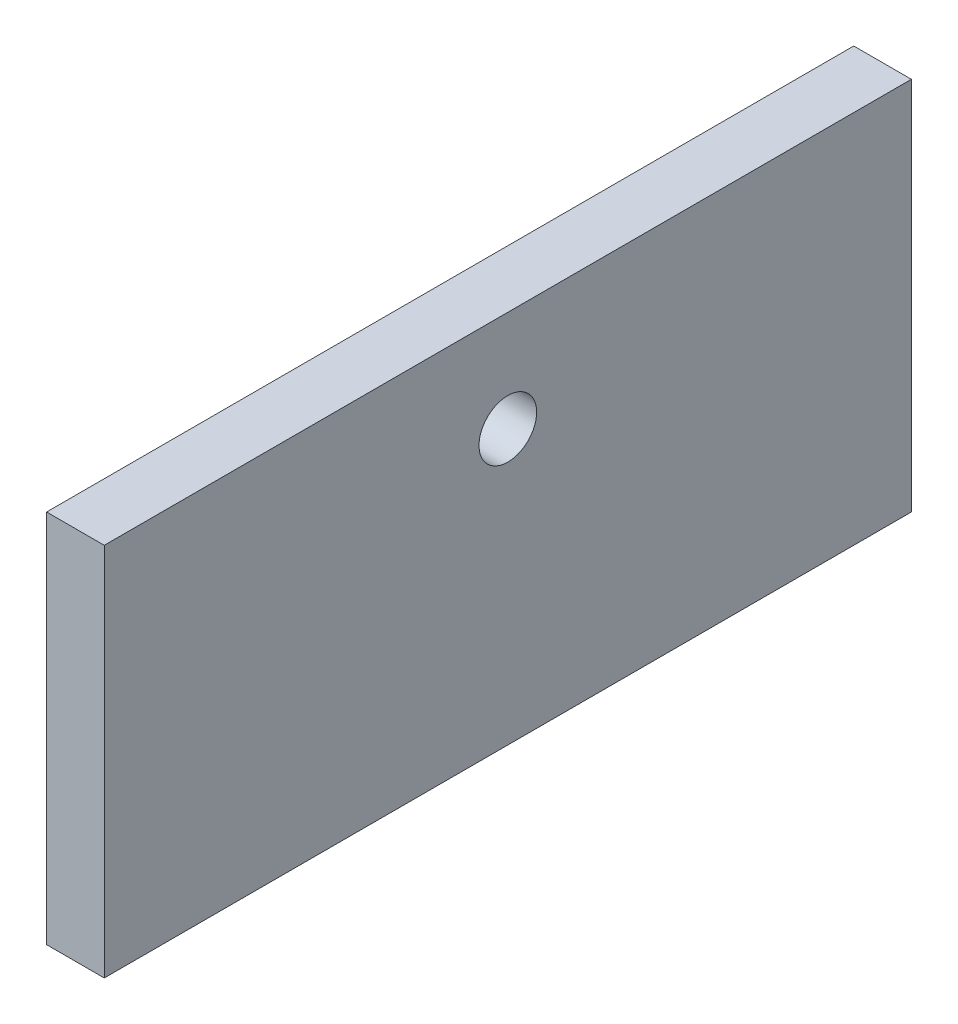
SolidWorks part; units mm, degrees
ref_plane "Front Plane" through (0, 0, 0) normal (0, 0, 1) x (1, 0, 0)
ref_plane "Top Plane" through (0, 0, 0) normal (0, 1, 0) x (1, 0, 0)
ref_plane "Right Plane" through (0, 0, 0) normal (1, 0, 0) x (0, 0, -1)
sketch "Croquis1" plane through (0, 0, 0) normal (1, 0, 0) x (0, 0, -1)
  line L0 (0, 0) -> (0, 25) construction
  circle A0 centre (0, 0) radius 30
  circle A1 centre (0, 0) radius 5
  circle A2 centre (0, 25) radius 2.5
  dimension "D1" = 60
  dimension "D2" = 5
  dimension "D3" = 10
  dimension "D4" = 25
extrude "Saliente-Extruir1" [suppressed] add sketch "Croquis1" along normal blind 10
sketch "Croquis3" plane through (0, 0, 0) normal (0, 0, 1) x (1, 0, 0)
  line L0 (270, 0) -> (-270, 0)
  line L1 (270, 0) -> (270, 5)
  line L2 (270, 5) -> (250, 5)
  line L3 (250, 5) -> (250, 9.5)
  line L4 (250, 9.5) -> (-250, 9.5)
  line L5 (-250, 9.5) -> (-250, 5)
  line L6 (-250, 5) -> (-270, 5)
  line L7 (-270, 5) -> (-270, 0)
  line L8 (-250, 5) -> (250, 5) construction
  point P4 (0, 0)
  dimension "D1" = 500
  dimension "D2" = 20
  dimension "D3" = 20
  dimension "D4" = 5
  dimension "D5" = 9.5
revolve "Revolución1" [suppressed] add sketch "Croquis3" angle 360 about L0
sketch "Croquis4" plane through (0, 0, 0) normal (1, 0, 0) x (0, 0, -1)
  line L1 (50, -30) -> (-50, -30)
  line L2 (50, -30) -> (50, 30)
  line L3 (50, 30) -> (-50, 30)
  line L4 (-50, -30) -> (-50, 30)
  line L5 (50, -30) -> (-50, 30) construction
  line L6 (50, 30) -> (-50, -30) construction
  circle A0 centre (0, 0) radius 9.5
  point P0 (0, 0)
  dimension "D3" = 19
  dimension "D1" = 100
  dimension "D2" = 60
extrude "Saliente-Extruir2" [suppressed] add sketch "Croquis4" along normal blind 50 contours L4 L1 L2 L3 A0
sketch "Croquis5" plane through (0, 0, 0) normal (1, 0, 0) x (0, 0, -1)
  line L0 (50, 0) -> (-50, 0)
  line L1 (-50, 0) -> (-50, 45)
  line L2 (-50, 45) -> (-70, 45)
  line L3 (-70, 45) -> (-70, -20)
  line L4 (-70, -20) -> (70, -20)
  line L5 (70, -20) -> (70, 45)
  line L6 (70, 45) -> (50, 45)
  line L7 (50, 45) -> (50, 0)
  point P4 (0, 0)
  dimension "D1" = 20
  dimension "D2" = 65
  dimension "D3" = 45
  dimension "D4" = 100
extrude "Saliente-Extruir3" [suppressed] add sketch "Croquis5" along normal blind 500
sketch "Croquis6" plane through (0, 0, 0) normal (1, 0, 0) x (0, 0, -1)
  line L0 (0, 0) -> (0, 15) construction
  line L1 (70, -32.5) -> (-70, -32.5)
  line L2 (70, -32.5) -> (70, 32.5)
  line L3 (70, 32.5) -> (-70, 32.5)
  line L4 (-70, -32.5) -> (-70, 32.5)
  line L5 (70, -32.5) -> (-70, 32.5) construction
  line L6 (70, 32.5) -> (-70, -32.5) construction
  circle A1 centre (0, 15) radius 5
  point P0 (0, 0)
  dimension "D3" = 10
  dimension "D1" = 140
  dimension "D2" = 65
  dimension "D4" = 15
extrude "Saliente-Extruir4" add sketch "Croquis6" along normal blind 10
sketch "Croquis7" [suppressed] plane through (0, 0, 0) normal (1, 0, 0) x (0, 0, -1)
  line L1 (50, -30) -> (-50, -30)
  line L2 (50, -30) -> (50, 30)
  line L3 (50, 30) -> (-50, 30)
  line L4 (-50, -30) -> (-50, 30)
  line L5 (50, -30) -> (-50, 30) construction
  line L6 (50, 30) -> (-50, -30) construction
  circle A0 centre (0, 3.1627) radius 9.5
  point P0 (0, 0)
  dimension "D3" = 19
  dimension "D1" = 100
  dimension "D2" = 60
extrude "Saliente-Extruir5" [suppressed] add sketch "Croquis7" along normal blind 50
